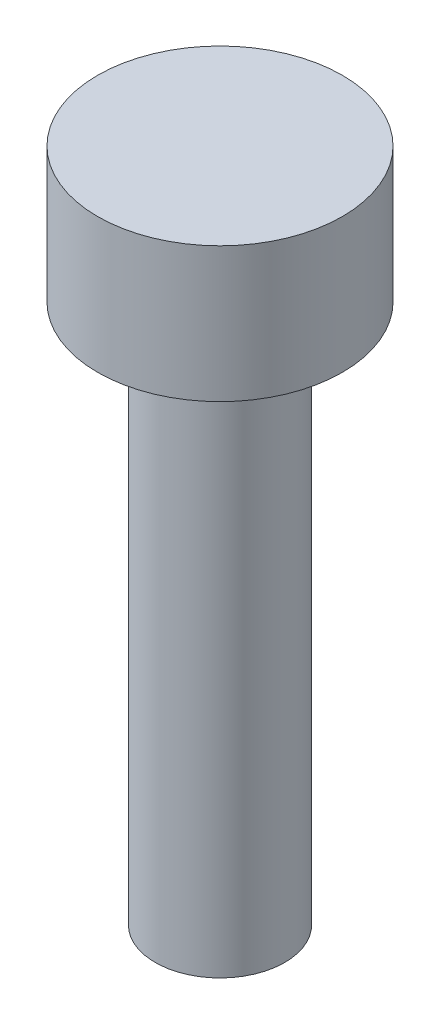
SolidWorks part; units mm, degrees
ref_plane "Front Plane" through (0, 0, 0) normal (0, 0, 1) x (1, 0, 0)
ref_plane "Top Plane" through (0, 0, 0) normal (0, 1, 0) x (1, 0, 0)
ref_plane "Right Plane" through (0, 0, 0) normal (1, 0, 0) x (0, 0, -1)
sketch "Sketch1" plane through (0, 0, 0) normal (0, 1, 0) x (1, 0, 0)
  circle A0 centre (0, 0) radius 2.72
  dimension "D1" = 5.44
extrude "Boss-Extrude1" add sketch "Sketch1" along normal blind 3
sketch "Sketch2" plane through (0, 0, 0) normal (0, -1, 0) x (1, 0, 0)
  circle A0 centre (0, 0) radius 1.44
  dimension "D1" = 2.88
extrude "Boss-Extrude2" add sketch "Sketch2" along normal blind 12
